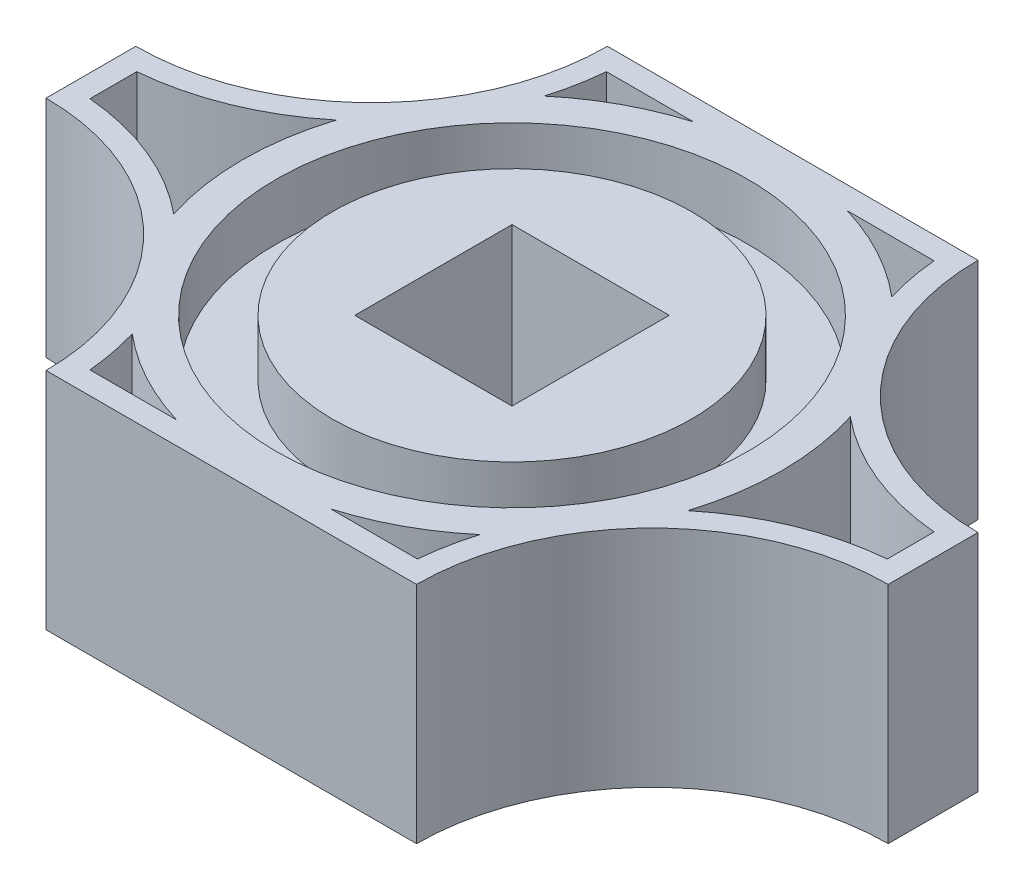
SolidWorks part; units mm, degrees
ref_plane "Front Plane" through (0, 0, 0) normal (0, 0, 1) x (1, 0, 0)
ref_plane "Top Plane" through (0, 0, 0) normal (0, 1, 0) x (1, 0, 0)
ref_plane "Right Plane" through (0, 0, 0) normal (1, 0, 0) x (0, 0, -1)
sketch "Sketch1" plane through (0, 0, 0) normal (0, 1, 0) x (1, 0, 0)
  line L1 (0, 0) -> (75, 0)
  line L2 (0, 0) -> (0, 50)
  line L3 (0, 50) -> (75, 50)
  line L4 (75, 0) -> (75, 50)
  dimension "D1" = 75
  dimension "D2" = 50
extrude "Boss-Extrude1" add sketch "Sketch1" along normal blind 20
sketch "Sketch2" plane through (0, 20, 0) normal (0, 1, 0) x (1, 0, 0)
  line L0 (37.5, 50) -> (37.5, 0) construction
  line L1 (0, 0) -> (75, 0) construction
  line L2 (0, 25) -> (75, 25) construction
  line L3 (0, 50) -> (0, 0) construction
  line L4 (75, 0) -> (75, 50) construction
  line L5 (75, 50) -> (0, 50) construction
  circle A0 centre (37.5, 25) radius 21
  circle A1 centre (37.5, 25) radius 16
  dimension "D1" = 42
  dimension "D2" = 32
extrude "Cut-Extrude1" cut sketch "Sketch2" against normal blind 5
sketch "Sketch3" plane through (0, 20, 0) normal (0, 1, 0) x (1, 0, 0)
  line L1 (30.5, 32) -> (44.5, 32)
  line L2 (30.5, 32) -> (30.5, 18)
  line L3 (30.5, 18) -> (44.5, 18)
  line L4 (44.5, 32) -> (44.5, 18)
  line L5 (30.5, 32) -> (44.5, 18) construction
  line L6 (30.5, 18) -> (44.5, 32) construction
  circle A0 centre (37.5, 25) radius 16 construction
  point P0 (37.5, 25)
  dimension "D1" = 14
  dimension "D2" = 14
extrude "Cut-Extrude2" cut sketch "Sketch3" against normal through all
sketch "Sketch4" plane through (0, 0, 0) normal (0, -1, 0) x (1, 0, 0)
  line L1 (37.5, 0) -> (37.5, -50) construction
  line L2 (0, 0) -> (75, 0) construction
  line L3 (75, -50) -> (0, -50) construction
  line L4 (0, -25) -> (75, -25) construction
  line L5 (0, -50) -> (0, 0) construction
  line L6 (75, 0) -> (75, -50) construction
  line L7 (0, -29) -> (0, -50)
  line L8 (0, -50) -> (21, -50)
  line L9 (75, -29) -> (75, -50)
  line L10 (75, -50) -> (54, -50)
  line L11 (75, -21) -> (75, 0)
  line L12 (75, 0) -> (54, 0)
  line L13 (0, 0) -> (21, 0)
  line L14 (0, -21) -> (0, 0)
  circle A0 centre (8.31, -25) radius 1.5875 construction
  circle A1 centre (66.69, -25) radius 1.5875 construction
  circle A2 centre (37.5, -25) radius 21 construction
  arc A3 (0, -29) -> (21, -50) centre (0, -50) cw
  arc A4 (75, -29) -> (54, -50) centre (75, -50) ccw
  arc A5 (75, -21) -> (54, 0) centre (75, 0) cw
  arc A6 (0, -21) -> (21, 0) centre (0, 0) ccw
  dimension "D2" = 3.175
  dimension "D3" = 42
  dimension "D4" = 21
  dimension "D1" = 29.19
extrude "Cut-Extrude3" cut sketch "Sketch4" against normal through all
sketch "Sketch6" plane through (0, 20, 0) normal (0, 1, 0) x (1, 0, 0)
  line L4 (30.6443, 48) -> (22.9129, 48)
  line L5 (44.3557, 2) -> (52.0871, 2)
  line L8 (2, 27.0871) -> (2, 22.9129)
  line L9 (22.9129, 2) -> (52.0871, 2)
  line L10 (73, 22.9129) -> (73, 27.0871)
  line L11 (52.0871, 48) -> (22.9129, 48)
  line L16 (2, 27.0871) -> (2, 22.9129)
  line L17 (22.9129, 2) -> (30.6443, 2)
  line L18 (73, 22.9129) -> (73, 27.0871)
  line L19 (52.0871, 48) -> (44.3557, 48)
  arc A18 (30.6443, 48) -> (22.013, 43.3344) centre (37.5, 25) ccw
  arc A19 (52.987, 43.3344) -> (44.3557, 48) centre (37.5, 25) ccw
  arc A20 (22.9129, 2) -> (2, 22.9129) centre (0, 0) ccw
  arc A21 (73, 22.9129) -> (52.0871, 2) centre (75, 0) ccw
  arc A22 (52.0871, 48) -> (73, 27.0871) centre (75, 50) ccw
  arc A23 (2, 27.0871) -> (22.9129, 48) centre (0, 50) ccw
  arc A24 (22.9129, 2) -> (22.013, 6.6656) centre (0, 0) ccw
  arc A25 (73, 22.9129) -> (60.3806, 17.756) centre (75, 0) ccw
  arc A26 (52.0871, 48) -> (52.987, 43.3344) centre (75, 50) ccw
  arc A27 (2, 27.0871) -> (14.6194, 32.244) centre (0, 50) ccw
  arc A28 (14.6194, 32.244) -> (14.6194, 17.756) centre (37.5, 25) ccw
  arc A29 (22.013, 43.3344) -> (22.9129, 48) centre (0, 50) ccw
  arc A30 (60.3806, 32.244) -> (73, 27.0871) centre (75, 50) ccw
  arc A31 (52.987, 6.6656) -> (52.0871, 2) centre (75, 0) ccw
  arc A32 (60.3806, 17.756) -> (60.3806, 32.244) centre (37.5, 25) ccw
  arc A33 (44.3557, 2) -> (52.987, 6.6656) centre (37.5, 25) ccw
  arc A34 (14.6194, 17.756) -> (2, 22.9129) centre (0, 0) ccw
  arc A35 (22.013, 6.6656) -> (30.6443, 2) centre (37.5, 25) ccw
  dimension "D1" = 2
extrude "Cut-Extrude6" cut sketch "Sketch6" along direction (0, -1, 0) on the side against the normal offset from surface (10 mm away) 10
